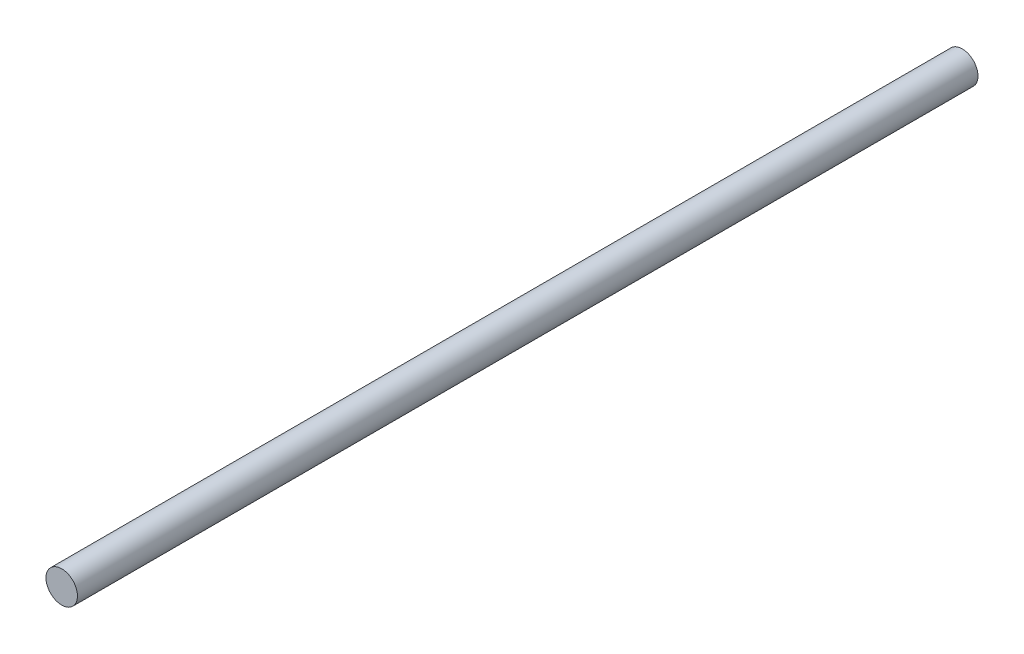
SolidWorks part; units mm, degrees
material "6061 Alloy"
ref_plane "Front Plane" through (0, 0, 0) normal (0, 0, 1) x (1, 0, 0)
ref_plane "Top Plane" through (0, 0, 0) normal (0, 1, 0) x (1, 0, 0)
ref_plane "Right Plane" through (0, 0, 0) normal (1, 0, 0) x (0, 0, -1)
sketch "Sketch1" plane through (0, 0, 0) normal (0, 0, 1) x (1, 0, 0)
  circle A0 centre (0, 0) radius 5
  dimension "D1" = 10
extrude "Boss-Extrude1" add sketch "Sketch1" along normal blind 286
